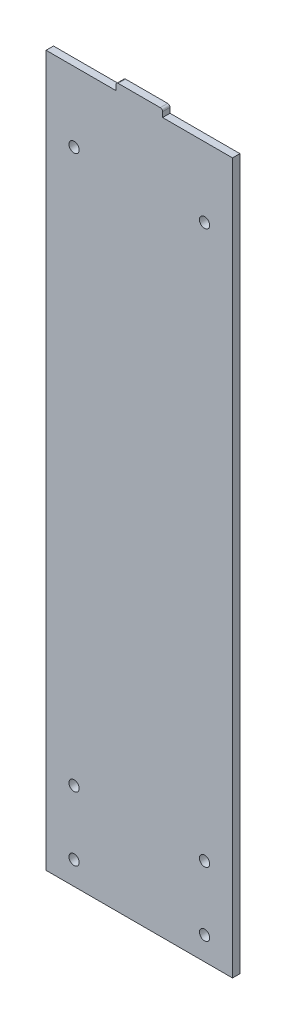
SolidWorks part; units mm, degrees
ref_plane "Front Plane" through (0, 0, 0) normal (0, 0, 1) x (1, 0, 0)
ref_plane "Top Plane" through (0, 0, 0) normal (0, 1, 0) x (1, 0, 0)
ref_plane "Right Plane" through (0, 0, 0) normal (1, 0, 0) x (0, 0, -1)
sketch "Sketch1" plane through (0, 0, 0) normal (0, 0, 1) x (1, 0, 0)
  line L1 (-40, -152.4) -> (40, -152.4)
  line L2 (-40, -152.4) -> (-40, 152.4)
  line L3 (-40, 152.4) -> (40, 152.4)
  line L4 (40, -152.4) -> (40, 152.4)
  line L5 (-40, -152.4) -> (40, 152.4) construction
  line L6 (-40, 152.4) -> (40, -152.4) construction
  point P0 (0, 0)
  dimension "D1" = 304.8
  dimension "D2" = 80
extrude "Boss-Extrude1" add sketch "Sketch1" along normal blind 3.175
sketch "Sketch2" plane through (0, 0, 3.175) normal (0, 0, 1) x (1, 0, 0)
  line L0 (-40, -104.9) -> (40, -104.9) construction
  line L1 (-40, 152.4) -> (-40, -152.4) construction
  line L2 (40, -152.4) -> (40, 152.4) construction
  line L3 (-40, -152.4) -> (40, -152.4) construction
  line L4 (0, -104.9) -> (0, -152.4) construction
  line L5 (0, -128.65) -> (7.2998, -128.65) construction
  line L6 (40, 152.4) -> (-40, 152.4) construction
  line L7 (0, 152.4) -> (0, 130.4264) construction
  circle A0 centre (-28, -114.9) radius 2.2
  circle A1 centre (28, -114.9) radius 2.2
  circle A2 centre (28, -142.4) radius 2.2
  circle A3 centre (-28, -142.4) radius 2.2
  circle A4 centre (-28, 122.4) radius 2.2
  circle A5 centre (28, 122.4) radius 2.2
  dimension "D2" = 4.4
  dimension "D5" = 4.4
  dimension "D1" = 47.5
  dimension "D3" = 28
  dimension "D4" = 10
  dimension "D6" = 12
  dimension "D7" = 30
extrude "Cut-Extrude1" cut sketch "Sketch2" against normal through all
sketch "Sketch3" plane through (0, 152.4, 0) normal (0, 1, 0) x (1, 0, 0)
  line L0 (0, 0) -> (0, -3.175) construction
  line L1 (40, -3.175) -> (-40, -3.175) construction
  line L2 (40, 0) -> (-40, 0) construction
  line L3 (-10, -3.175) -> (10, -3.175)
  line L4 (-10, -3.175) -> (-10, 0)
  line L5 (-10, 0) -> (10, 0)
  line L6 (10, -3.175) -> (10, 0)
  line L7 (-10, -3.175) -> (10, 0) construction
  line L8 (-10, 0) -> (10, -3.175) construction
  point P5 (0, -1.5875)
  dimension "D1" = 20
extrude "Boss-Extrude2" add sketch "Sketch3" along normal blind 3.175
fillet "Fillet1" radius 1 2 edges at (10, 155.575, 1.5875) (-10, 155.575, 1.5875)
